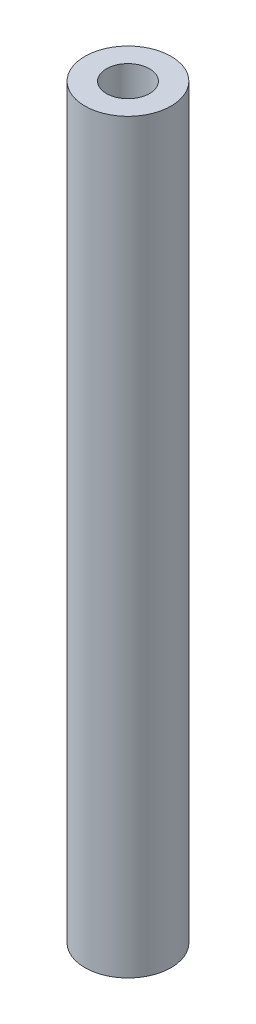
SolidWorks part; units mm, degrees
ref_plane "Front Plane" through (0, 0, 0) normal (0, 0, 1) x (1, 0, 0)
ref_plane "Top Plane" through (0, 0, 0) normal (0, 1, 0) x (1, 0, 0)
ref_plane "Right Plane" through (0, 0, 0) normal (1, 0, 0) x (0, 0, -1)
sketch "Sketch1" plane through (0, 0, 0) normal (0, 1, 0) x (1, 0, 0)
  circle A0 centre (0, 0) radius 1.5875
  circle A1 centre (0, 0) radius 0.7937
  dimension "D1" = 3.175
  dimension "D2" = 1.5875
extrude "Boss-Extrude1" add sketch "Sketch1" along normal blind 27.5
